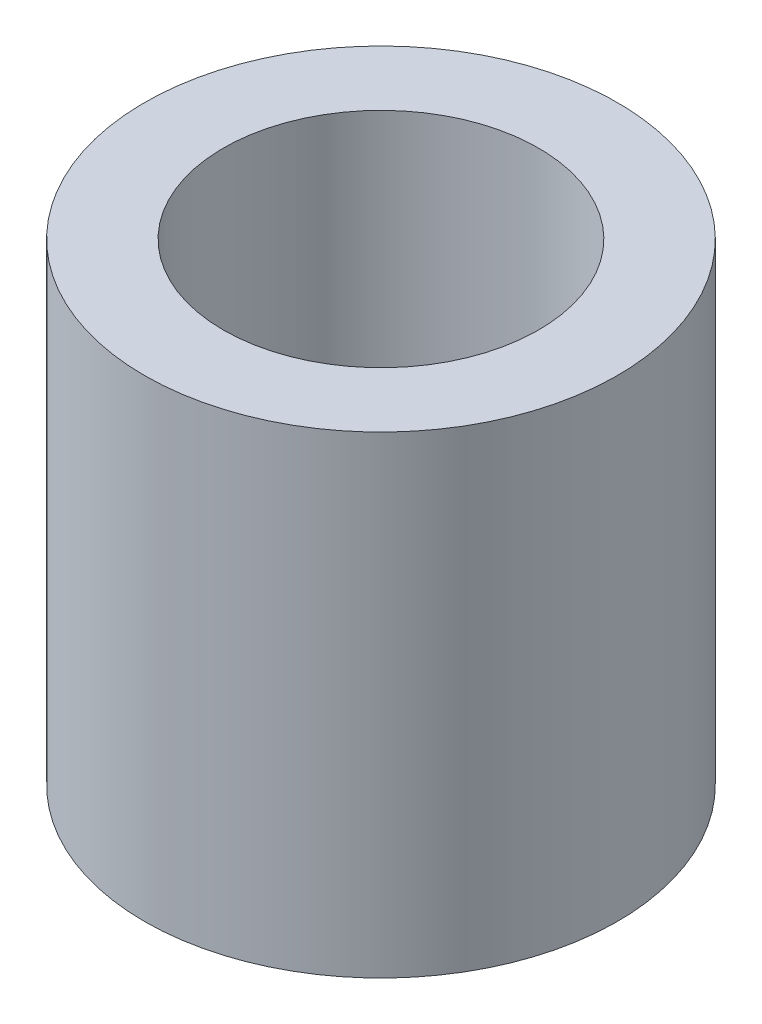
SolidWorks part; units mm, degrees
ref_plane "Front Plane" through (0, 0, 0) normal (0, 0, 1) x (1, 0, 0)
ref_plane "Top Plane" through (0, 0, 0) normal (0, 1, 0) x (1, 0, 0)
ref_plane "Right Plane" through (0, 0, 0) normal (1, 0, 0) x (0, 0, -1)
sketch "Sketch1" plane through (0, 0, 0) normal (0, 1, 0) x (1, 0, 0)
  circle A0 centre (0, 0) radius 3
  circle A1 centre (0, 0) radius 2
  dimension "D1" = 6
  dimension "D2" = 4
extrude "Boss-Extrude1" add sketch "Sketch1" along normal blind 6
